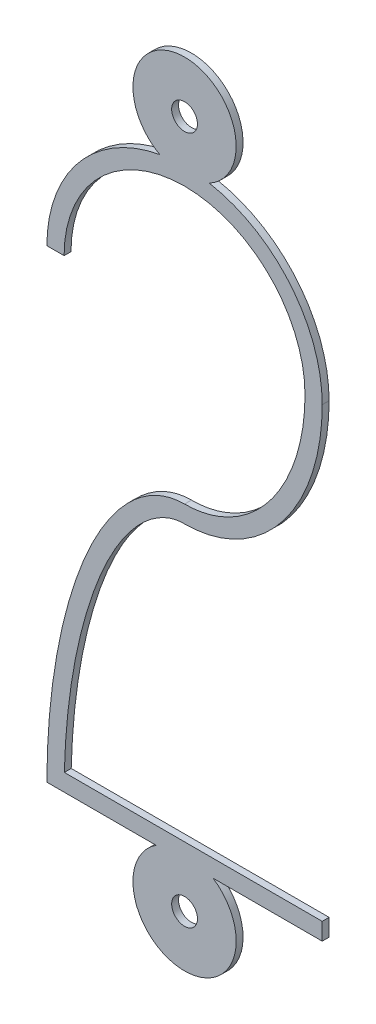
SolidWorks part; units mm, degrees
material "3.0517 (EN-AW 3003)"
ref_plane "Front Plane" through (0, 0, 0) normal (0, 0, 1) x (1, 0, 0)
ref_plane "Top Plane" through (0, 0, 0) normal (0, 1, 0) x (1, 0, 0)
ref_plane "Right Plane" through (0, 0, 0) normal (1, 0, 0) x (0, 0, -1)
sketch "Sketch1" plane through (0, 0, 0) normal (0, 0, 1) x (1, 0, 0)
  line L0 (0, 10) -> (0, -10) construction
  line L1 (-4, -8.75) -> (-0.8292, -8.75)
  line L2 (4, -8.75) -> (4, -8.25)
  line L3 (4, -8.25) -> (-3.4937, -8.25)
  line L4 (0.8292, -8.75) -> (4, -8.75)
  line L5 (0, 0.25) -> (0, -0.25) construction
  line L6 (-4, 8.75) -> (4, 8.75) construction
  line L7 (-4, 8.75) -> (-4, 4.75) construction
  line L8 (4, 8.75) -> (4, 4.75) construction
  line L9 (-4, 4.75) -> (-3.5, 4.75)
  arc A0 (0.7208, 8.6845) -> (-0.7208, 8.6845) centre (0, 10) ccw
  circle A1 centre (0, 10) radius 0.375
  arc A2 (-0.8292, -8.75) -> (0.8292, -8.75) centre (0, -10) ccw
  circle A3 centre (0, -10) radius 0.375
  arc A4 (-4, 4.75) -> (-0.7208, 8.6845) centre (0, 4.75) cw
  arc A5 (-3.5, 4.75) -> (3.5, 4.75) centre (0, 4.75) cw
  arc A6 (0.7208, 8.6845) -> (4, 4.75) centre (0, 4.75) cw
  arc A7 (-4, 4.75) -> (4, 4.75) centre (0, 4.75) cw construction
  ellipse E0 centre (0, -8.75) end of major axis (0, 0.25) minor radius 4 (0, 0.25) -> (-4, -8.75) ccw
  ellipse E1 centre (0, 4.75) end of major axis (0, 9.75) minor radius 4 (0, -0.25) -> (4, 4.75) ccw
  ellipse E2 centre (0, 4.75) end of major axis (0, 9.25) minor radius 3.5 (0, 0.25) -> (3.5, 4.75) ccw
  spline S0 degree 1 poles (0, -0.25) (-3.5, -8.75) knots 0 0 1 1 construction
  spline S1 degree 3 poles (0, -0.25) (-0.1968, -0.25) (-0.5632, -0.3301) (-1.1903, -0.7456) (-1.8145, -1.4927) (-2.5782, -2.8965) (-3.1527, -4.8228) (-3.4496, -7.025) (-3.5, -8.1789) (-3.5, -8.75) knots 3.141593 3.141593 3.141593 3.141593 3.337942 3.534292 3.730641 3.926991 4.31969 4.516039 4.712389 4.712389 4.712389 4.712389 only from (0, -0.25) to (-3.4937, -8.25)
  point P24 (0, 8.75)
  dimension "D2" = 3
  dimension "D3" = 0.75
  dimension "D4" = 1.25
  dimension "D5" = 8
  dimension "D7" = 0.5
  dimension "D8" = 1.25
  dimension "D1" = 20
  dimension "D6" = 0.5
  dimension "D9" = 0.5
extrude "Boss-Extrude1" add sketch "Sketch1" along normal mid plane 0.2
sketch "Sketch2" plane through (0, 0, 0) normal (0, 0, 1) x (1, 0, 0)
  line L10 (-4.2485, -9) -> (-1.4361, -9)
  line L11 (1.4361, -9) -> (4.25, -9)
  line L12 (4.25, -9) -> (4.25, -8)
  line L13 (4.25, -8) -> (-3.2355, -8)
  line L14 (-4.2426, 4.5) -> (-3.2404, 4.5)
  line L15 (-4.2485, -9) -> (0, -9)
  line L16 (0, -9) -> (4.25, -9)
  line L17 (4.25, -9) -> (4.25, -8)
  line L18 (4.25, -8) -> (-3.2355, -8)
  line L19 (-4.2426, 4.5) -> (-3.2404, 4.5)
  arc A10 (-1.4361, -9) -> (1.4361, -9) centre (0, -10) ccw
  arc A11 (4.25, 4.75) -> (1.2771, 8.8036) centre (0, 4.75) ccw
  arc A12 (1.2771, 8.8036) -> (-1.2771, 8.8036) centre (0, 10) ccw
  arc A13 (-1.2771, 8.8036) -> (-4.2426, 4.5) centre (0, 4.75) ccw
  arc A14 (3.25, 4.75) -> (-3.2404, 4.5) centre (0, 4.75) ccw
  arc A16 (4.25, 4.75) -> (0, 9) centre (0, 4.75) ccw
  arc A18 (0, 9) -> (-4.2426, 4.5) centre (0, 4.75) ccw
  arc A19 (3.25, 4.75) -> (-3.2404, 4.5) centre (0, 4.75) ccw
  spline S2 degree 3 poles (804.6665, -3916.8179) (84.5931, -238.4741) (17.9797, 6.8806) (-0.9178, 0.3023) (-1.1272, 0.1903) (-1.5141, -0.078) (-1.6937, -0.2361) (-2.0192, -0.5741) (-2.1673, -0.7557) (-2.4421, -1.1374) (-2.5687, -1.3382) (-2.8002, -1.7463) (-2.9059, -1.9548) (-3.1989, -2.5906) (-3.3627, -3.0282) (-3.6444, -3.9236) (-3.761, -4.3791) (-3.9537, -5.2912) (-4.0302, -5.7498) (-17.8492, -112.9311) (870.6012, -333.7701) (-3985.918, 172.0592) knots -5.147538 -5.147538 -5.147538 -5.147538 0.0625 0.0625 0.125 0.125 0.1875 0.1875 0.25 0.25 0.3125 0.3125 0.375 0.375 0.5 0.5 0.625 0.625 0.75 0.75 29.703229 29.703229 29.703229 29.703229 only from (0, 0.5) to (-4.2485, -9)
  spline S3 degree 3 poles (-3955.5254, 571.1853) (427.923, -240.3231) (-14.3062, -77.2977) (-2.9176, -5.151) (-2.7624, -4.454) (-2.439, -3.4269) (-2.3158, -3.0873) (-2.0251, -2.4184) (-1.8604, -2.0948) (-1.5691, -1.634) (-1.4639, -1.4839) (-1.2354, -1.1998) (-1.1125, -1.0656) (-0.8389, -0.8225) (-0.6908, -0.7153) (-0.4457, -0.592) (-0.36, -0.5575) (9.0967, 1.9213) (63.0455, -127.8501) (-3995.839, -98.1339) knots -25.054931 -25.054931 -25.054931 -25.054931 0.25 0.25 0.5 0.5 0.625 0.625 0.75 0.75 0.8125 0.8125 0.875 0.875 0.9375 0.9375 0.96875 0.96875 4.299138 4.299138 4.299138 4.299138 only from (-3.2355, -8) to (0, -0.5)
  spline S4 degree 3 poles (-775.9744, 3922.649) (-128.6818, 382.2856) (-29.1672, -8.6231) (1.0732, -0.3339) (1.2226, -0.2822) (1.5108, -0.1615) (1.6502, -0.0926) (2.0552, 0.1386) (2.3098, 0.3272) (2.7682, 0.7486) (2.9747, 0.9826) (3.3441, 1.4896) (3.503, 1.7569) (3.7757, 2.3157) (3.89, 2.6095) (4.0705, 3.2054) (4.1374, 3.5083) (8.1744, 31.1445) (-162.7824, 104.9629) (-945.5894, -3875.6959) knots -12.389819 -12.389819 -12.389819 -12.389819 0.125 0.125 0.1875 0.1875 0.25 0.25 0.375 0.375 0.5 0.5 0.625 0.625 0.75 0.75 0.875 0.875 11.985026 11.985026 11.985026 11.985026 only from (0, -0.5) to (4.25, 4.75)
  spline S5 degree 3 poles (3968.751, -469.7375) (-1227.934, 349.1056) (21.1492, 68.0899) (2.9872, 3.0599) (2.903, 2.8248) (2.7014, 2.3763) (2.5838, 2.1613) (2.3104, 1.752) (2.1532, 1.557) (1.8065, 1.2081) (1.6151, 1.0515) (1.1942, 0.7869) (0.9713, 0.6827) (-16.8568, -4.7499) (-92.9469, 177.1872) (3284.4191, 2273.0582) knots -33.984785 -33.984785 -33.984785 -33.984785 0.25 0.25 0.375 0.375 0.5 0.5 0.625 0.625 0.75 0.75 0.875 0.875 10.15277 10.15277 10.15277 10.15277 only from (3.25, 4.75) to (0, 0.5)
  spline S6 degree 3 poles (0, 0.5) (-0.2389, 0.5) (-0.4698, 0.4583) (-0.9178, 0.3023) (-1.1272, 0.1903) (-1.5141, -0.078) (-1.6937, -0.2361) (-2.0192, -0.5741) (-2.1673, -0.7557) (-2.4421, -1.1374) (-2.5687, -1.3382) (-2.8002, -1.7463) (-2.9059, -1.9548) (-3.1989, -2.5906) (-3.3627, -3.0282) (-3.6444, -3.9236) (-3.761, -4.3791) (-3.9537, -5.2912) (-4.0302, -5.7498) (-4.2084, -7.132) (-4.2599, -8.062) (-4.2485, -9) knots 0 0 0 0 0.0625 0.0625 0.125 0.125 0.1875 0.1875 0.25 0.25 0.3125 0.3125 0.375 0.375 0.5 0.5 0.625 0.625 0.75 0.75 1 1 1 1
  spline S7 degree 3 poles (-3.2355, -8) (-3.2075, -7.2773) (-3.1404, -6.5626) (-2.9176, -5.151) (-2.7624, -4.454) (-2.439, -3.4269) (-2.3158, -3.0873) (-2.0251, -2.4184) (-1.8604, -2.0948) (-1.5691, -1.634) (-1.4639, -1.4839) (-1.2354, -1.1998) (-1.1125, -1.0656) (-0.8389, -0.8225) (-0.6908, -0.7153) (-0.4457, -0.592) (-0.36, -0.5575) (-0.1842, -0.5114) (-0.0923, -0.5) (0, -0.5) knots 0 0 0 0 0.25 0.25 0.5 0.5 0.625 0.625 0.75 0.75 0.8125 0.8125 0.875 0.875 0.9375 0.9375 0.96875 0.96875 1 1 1 1
  spline S8 degree 3 poles (0, -0.5) (0.3149, -0.5) (0.6223, -0.4574) (1.0732, -0.3339) (1.2226, -0.2822) (1.5108, -0.1615) (1.6502, -0.0926) (2.0552, 0.1386) (2.3098, 0.3272) (2.7682, 0.7486) (2.9747, 0.9826) (3.3441, 1.4896) (3.503, 1.7569) (3.7757, 2.3157) (3.89, 2.6095) (4.0705, 3.2054) (4.1374, 3.5083) (4.2272, 4.1232) (4.25, 4.4366) (4.25, 4.75) knots 0 0 0 0 0.125 0.125 0.1875 0.1875 0.25 0.25 0.375 0.375 0.5 0.5 0.625 0.625 0.75 0.75 0.875 0.875 1 1 1 1
  spline S9 degree 3 poles (3.25, 4.75) (3.25, 4.2543) (3.1854, 3.7696) (2.9872, 3.0599) (2.903, 2.8248) (2.7014, 2.3763) (2.5838, 2.1613) (2.3104, 1.752) (2.1532, 1.557) (1.8065, 1.2081) (1.6151, 1.0515) (1.1942, 0.7869) (0.9713, 0.6827) (0.4973, 0.5382) (0.2497, 0.5) (0, 0.5) knots 0 0 0 0 0.25 0.25 0.375 0.375 0.5 0.5 0.625 0.625 0.75 0.75 0.875 0.875 1 1 1 1
  dimension "D1" = 0.25
extrude "Boss-Extrude2" [suppressed] add sketch "Sketch2" along normal mid plane 0.6
